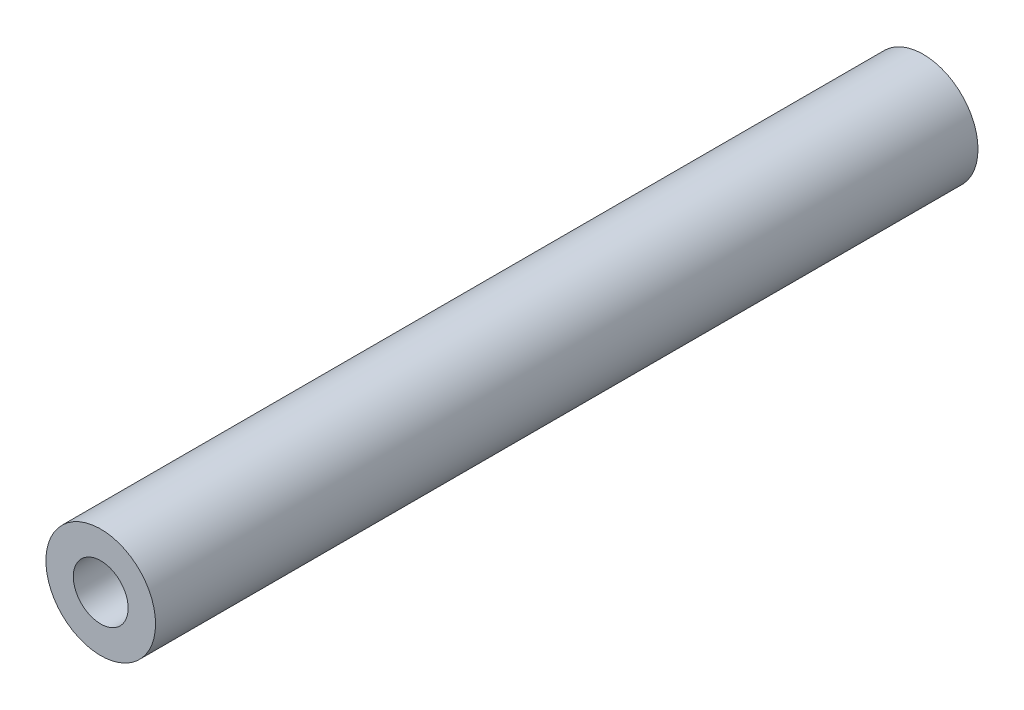
SolidWorks part; units mm, degrees
ref_plane "前视基准面" through (0, 0, 0) normal (0, 0, 1) x (1, 0, 0)
ref_plane "上视基准面" through (0, 0, 0) normal (0, 1, 0) x (1, 0, 0)
ref_plane "右视基准面" through (0, 0, 0) normal (1, 0, 0) x (0, 0, -1)
sketch "草图1" plane through (0, 0, 0) normal (0, 0, 1) x (1, 0, 0)
  circle A0 centre (0, 0) radius 3
  circle A1 centre (0, 0) radius 1.5
  dimension "D1" = 3
  dimension "D2" = 6
extrude "凸台-拉伸1" add sketch "草图1" along normal mid plane 45
